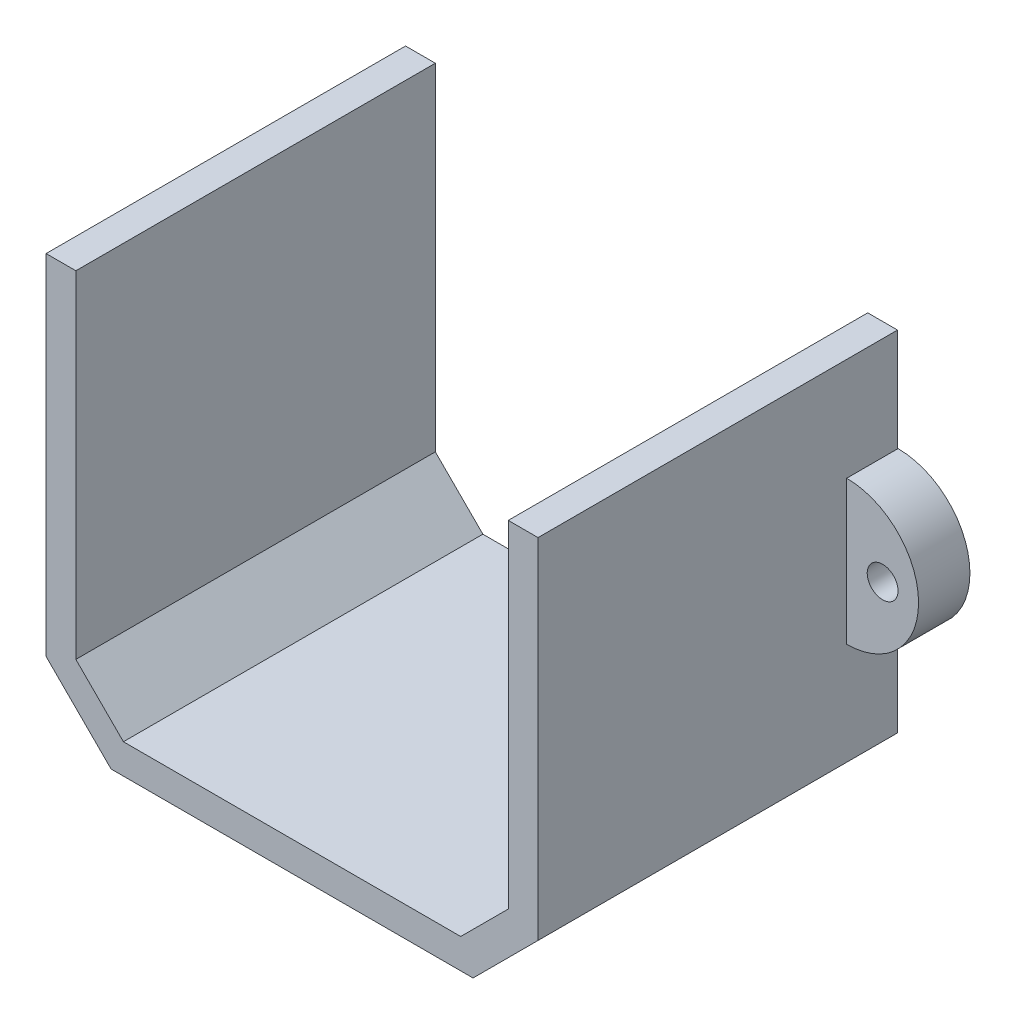
SolidWorks part; units mm, degrees
material "ABS"
ref_plane "Front Plane" through (0, 0, 0) normal (0, 0, 1) x (1, 0, 0)
ref_plane "Top Plane" through (0, 0, 0) normal (0, 1, 0) x (1, 0, 0)
ref_plane "Right Plane" through (0, 0, 0) normal (1, 0, 0) x (0, 0, -1)
sketch "Sketch1" plane through (0, 0, 0) normal (0, 0, 1) x (1, 0, 0)
  line L17 (21.1083, 144.2392) -> (21.1083, 177.0099)
  line L18 (21.1083, 177.0099) -> (24.0083, 177.0099)
  line L19 (24.0083, 143.038) -> (24.0083, 177.0099)
  line L20 (24.0083, 143.038) -> (17.6802, 136.7099)
  line L21 (-17.5637, 136.7099) -> (17.6802, 136.7099)
  line L22 (-17.5637, 136.7099) -> (-23.8917, 143.038)
  line L23 (-23.8917, 177.0099) -> (-23.8917, 143.038)
  line L24 (-23.8917, 177.0099) -> (-20.9917, 177.0099)
  line L25 (-20.9917, 177.0099) -> (-20.9917, 144.2392)
  line L26 (-16.3624, 139.6099) -> (-20.9917, 144.2392)
  line L27 (-16.3624, 139.6099) -> (16.479, 139.6099)
  line L28 (21.1083, 144.2392) -> (16.479, 139.6099)
  line L29 (21.1083, 177.0099) -> (21.1083, 177.0599)
extrude "Boss-Extrude1" add sketch "Sketch1" along normal blind 35 contours L17 L28 L27 L26 L25 L24 L23 L22 L21 L20 L19 L18
sketch "Sketch2" plane through (0, 0, 0) normal (0, 0, 1) x (1, 0, 0)
  line L0 (-23.9417, 177.0599) -> (-23.9417, 143.0173) construction
  line L1 (-23.9417, 167.0386) -> (-23.9417, 153.0386)
  line L2 (-23.9417, 160.0386) -> (-30.9417, 160.0386) construction
  line L3 (-21.9417, 151.2636) -> (-21.9417, 168.8136)
  line L4 (-23.9417, 153.0386) -> (-23.9417, 167.0386)
  line L5 (24.0583, 160.0386) -> (31.0583, 160.0386) construction
  line L6 (22.0583, 168.8136) -> (22.0583, 151.2636)
  line L7 (24.0583, 153.0386) -> (24.0583, 167.0386)
  line L8 (-21.9417, 168.8136) -> (-21.9417, 151.2636)
  line L9 (0.0583, 160.6599) -> (0.0583, 175.297) construction
  line L10 (22.0583, 151.2636) -> (22.0583, 168.8136)
  line L11 (24.0583, 167.0386) -> (24.0583, 153.0386)
  arc A0 (-23.9417, 167.0386) -> (-23.9417, 153.0386) centre (-23.9417, 160.0386) ccw
  circle A1 centre (-27.4417, 160.0386) radius 1.5
  arc A2 (22.0583, 168.8136) -> (22.0583, 151.2636) centre (24.0583, 160.0386) cw
  circle A3 centre (27.5583, 160.0386) radius 1.5
  arc A4 (24.0583, 167.0386) -> (24.0583, 153.0386) centre (24.0583, 160.0386) cw
  arc A7 (-21.9417, 168.8136) -> (-21.9417, 151.2636) centre (-23.9417, 160.0386) ccw
  dimension "D1" = 14
  dimension "D3" = 3
  dimension "D2" = 2
extrude "Boss-Extrude2" add sketch "Sketch2" along normal blind 5 contours A4 L7 A3 | L1 A0 A1
